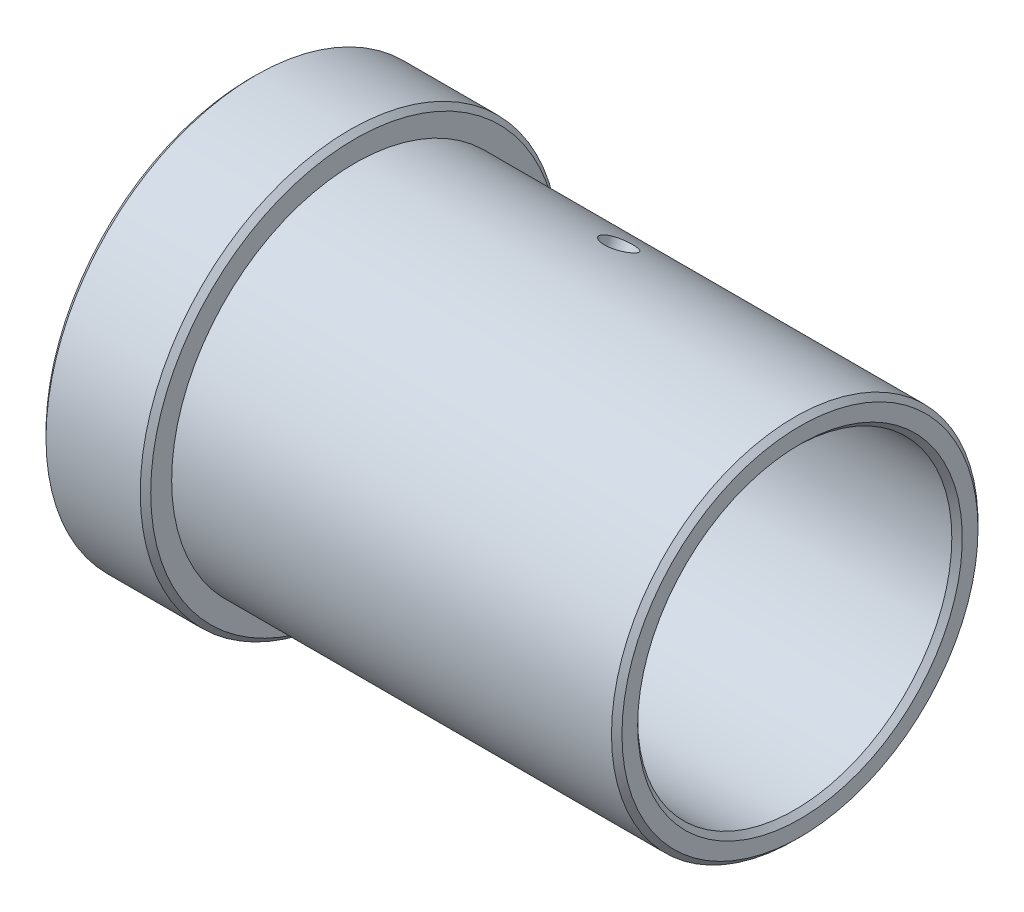
SolidWorks part; units mm, degrees
ref_plane "Спереди" through (0, 0, 0) normal (0, 0, 1) x (1, 0, 0)
ref_plane "Сверху" through (0, 0, 0) normal (0, 1, 0) x (1, 0, 0)
ref_plane "Справа" through (0, 0, 0) normal (1, 0, 0) x (0, 0, -1)
other "Configuration Table"
sketch "Эскиз1" plane through (0, 0, 0) normal (0, 0, 1) x (1, 0, 0)
  line L13 (0, 40) -> (0, 30)
  line L14 (0, 30) -> (105, 30)
  line L15 (105, 30) -> (105, 35)
  line L16 (105, 35) -> (20, 35)
  line L17 (20, 35) -> (20, 40)
  line L18 (20, 40) -> (0, 40)
  line L19 (0, 0) -> (96.7868, 0) construction
  line L20 (0, 0) -> (0, 43.9044) construction
  dimension "D1" = 0
  dimension "D2" = 20
  dimension "D3" = 80
  dimension "D4" = 70
  dimension "D5" = 60
  dimension "D6" = 105
revolve "Повернуть1" add sketch "Эскиз1" angle 360 about L19
chamfer "Фаска1" distance 1 angle 45 5 edges at (0, 0, 40) (0, 0, 30) (20, 0, 40) (105, 0, 30) (105, 0, 35)
extrude "Вырез-Вытянуть1" cut sketch "Эскиз2" against normal blind 108 and the other way blind 10
sketch "Эскиз2" plane through (110, 102, -50) normal (0, 0.8979, -0.4402) x (1, 0, 0)
  circle A0 centre (-55, 0) radius 3
